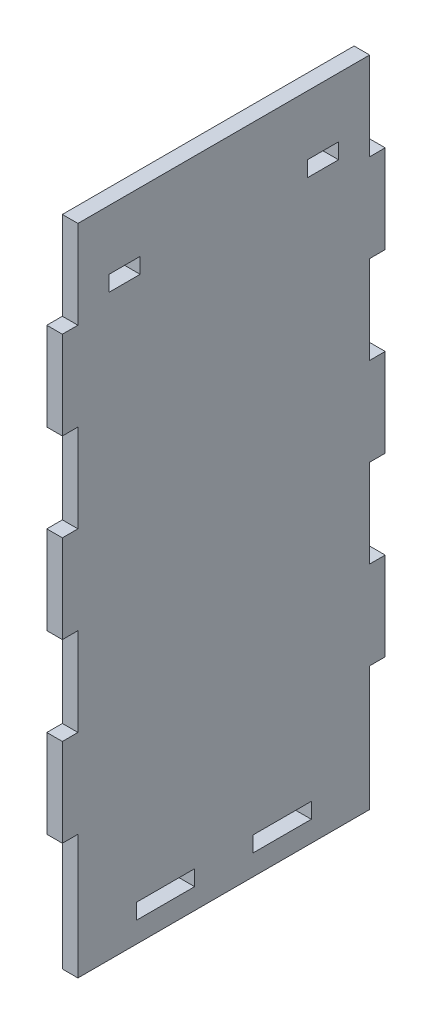
SolidWorks part; units mm, degrees
ref_plane "Front Plane" through (0, 0, 0) normal (0, 0, 1) x (1, 0, 0)
ref_plane "Top Plane" through (0, 0, 0) normal (0, 1, 0) x (1, 0, 0)
ref_plane "Right Plane" through (0, 0, 0) normal (1, 0, 0) x (0, 0, -1)
sketch "Sketch1" plane through (0, 0, 0) normal (1, 0, 0) x (0, 0, -1)
  line L1 (-56.25, -119) -> (56.25, -119)
  line L2 (-56.25, -119) -> (-56.25, 119)
  line L3 (-56.25, 119) -> (56.25, 119)
  line L4 (56.25, -119) -> (56.25, 119)
  line L5 (-56.25, -119) -> (56.25, 119) construction
  line L6 (-56.25, 119) -> (56.25, -119) construction
  point P0 (0, 0)
  dimension "D1" = 238
  dimension "D2" = 112.5
extrude "Boss-Extrude1" add sketch "Sketch1" along normal blind 6
sketch "Sketch4" plane through (0, -119, 0) normal (0, -1, 0) x (1, 0, 0)
  line L0 (6, 56.25) -> (6, -56.25) construction
  line L1 (0, -56.25) -> (6, -56.25)
  line L2 (0, -56.25) -> (0, -33.75)
  line L3 (0, -33.75) -> (6, -33.75)
  line L4 (6, -56.25) -> (6, -33.75)
  line L5 (0, 56.25) -> (0, -56.25) construction
  line L6 (6, -33.75) -> (0, -33.75) construction
  line L7 (6, -33.75) -> (6, -11.25) construction
  line L8 (6, -11.25) -> (0, -11.25) construction
  line L9 (0, -33.75) -> (0, -11.25) construction
  line L11 (6, 11.25) -> (0, 11.25)
  line L12 (6, 11.25) -> (6, -11.25)
  line L13 (6, -11.25) -> (0, -11.25)
  line L14 (0, 11.25) -> (0, -11.25)
  line L15 (0, 11.25) -> (6, 11.25) construction
  line L16 (0, 11.25) -> (0, 33.75) construction
  line L17 (0, 33.75) -> (6, 33.75) construction
  line L18 (6, 11.25) -> (6, 33.75) construction
  line L19 (6, 33.75) -> (0, 33.75)
  line L20 (6, 33.75) -> (6, 56.25)
  line L21 (6, 56.25) -> (0, 56.25)
  line L22 (0, 33.75) -> (0, 56.25)
extrude "Boss-Extrude2" add sketch "Sketch4" along normal blind 6
sketch "Sketch5" plane through (0, 0, -56.25) normal (0, 0, -1) x (-1, 0, 0)
  line L0 (0, -125) -> (0, 119) construction
  line L1 (-6, -119) -> (0, -119)
  line L2 (-6, -119) -> (-6, -85)
  line L3 (-6, -85) -> (0, -85)
  line L4 (0, -119) -> (0, -85)
  line L5 (-6, -125) -> (-6, 119) construction
  line L6 (0, -85) -> (-6, -85)
  line L7 (0, -85) -> (0, -51)
  line L8 (0, -51) -> (-6, -51)
  line L9 (-6, -85) -> (-6, -51)
  line L10 (-6, -119) -> (-6, -125) construction
  line L11 (-6, -51) -> (0, -51)
  line L12 (-6, -51) -> (-6, -17)
  line L13 (-6, -17) -> (0, -17)
  line L14 (0, -51) -> (0, -17)
  line L15 (0, -17) -> (-6, -17)
  line L16 (0, -17) -> (0, 17)
  line L17 (0, 17) -> (-6, 17)
  line L18 (-6, -17) -> (-6, 17)
  line L19 (-6, 17) -> (0, 17)
  line L20 (-6, 17) -> (-6, 51)
  line L21 (-6, 51) -> (0, 51)
  line L22 (0, 17) -> (0, 51)
  line L23 (0, 51) -> (-6, 51)
  line L24 (0, 51) -> (0, 85)
  line L25 (0, 85) -> (-6, 85)
  line L26 (-6, 51) -> (-6, 85)
  line L27 (-6, 85) -> (0, 85)
  line L28 (-6, 85) -> (-6, 119)
  line L29 (-6, 119) -> (0, 119)
  line L30 (0, 85) -> (0, 119)
  line L31 (0, -125) -> (-6, -125) construction
  line M17 (0, -125) -> (0, 119)
  line M19 (-6, 119) -> (-6, -125)
extrude "Boss-Extrude3" add sketch "Sketch5" along normal blind 6 contours L8 L3 M17 M19 | L17 L13 M17 M19 | L25 L21 M17 M19
mirror "Mirror1" about plane through (0, 0, 0) normal (0, 0, 1) of "Boss-Extrude3"
sketch "Sketch6" plane through (6, 0, 0) normal (1, 0, 0) x (0, 0, -1)
  line L0 (-32.25, 90) -> (32.25, 90)
  line L1 (-44.25, 90) -> (-32.25, 90)
  line L2 (-44.25, 90) -> (-44.25, 96)
  line L3 (-44.25, 96) -> (-32.25, 96)
  line L4 (-32.25, 90) -> (-32.25, 96)
  line L5 (32.25, 96) -> (44.25, 96)
  line L6 (32.25, 96) -> (32.25, 90)
  line L7 (32.25, 90) -> (44.25, 90)
  line L8 (44.25, 96) -> (44.25, 90)
  line L9 (0, 90) -> (0, 0)
  line L10 (-44.25, 90) -> (-44.25, 96) construction
  line L11 (-32.25, 96) -> (-44.25, 96) construction
  line L12 (32.25, 90) -> (-32.25, 90) construction
  line L13 (56.25, 119) -> (-56.25, 119) construction
  dimension "D1" = 23
extrude "Cut-Extrude1" cut sketch "Sketch6" against normal blind 800 contours L1 L4 L3 L2 | L8 L5 L6 L7
sketch "Sketch7" plane through (0, -125, 0) normal (0, -1, 0) x (1, 0, 0)
  line L1 (0, 56.25) -> (6, 56.25)
  line L2 (0, 56.25) -> (0, -56.25)
  line L3 (0, -56.25) -> (6, -56.25)
  line L4 (6, 56.25) -> (6, -56.25)
extrude "Boss-Extrude4" add sketch "Sketch7" along normal blind 8
